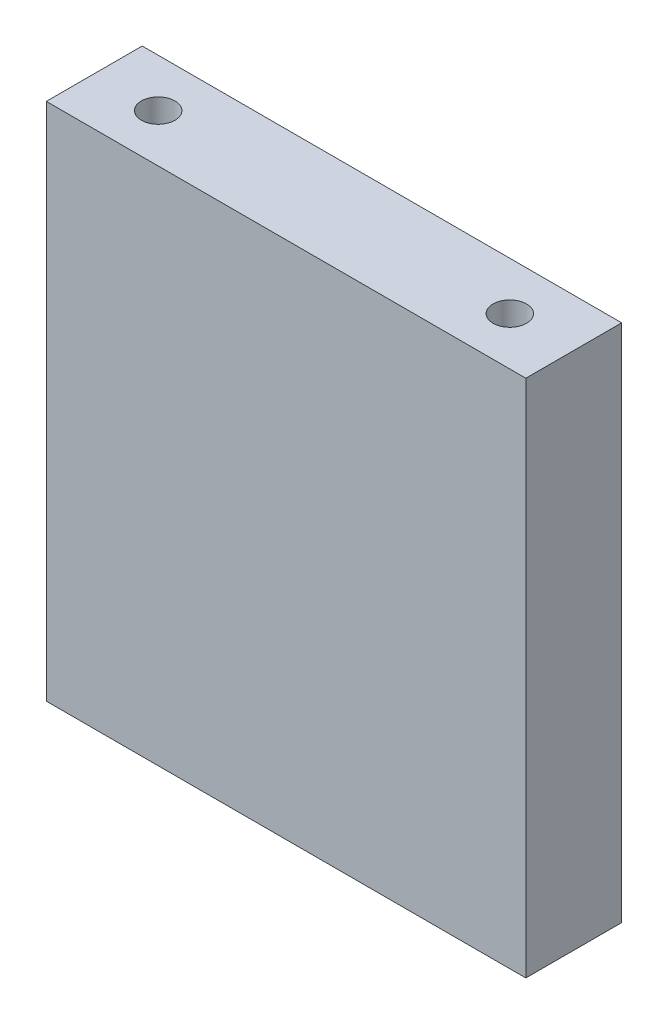
SolidWorks part; units mm, degrees
material "3.1325 (EN-AW 2017A)"
ref_plane "Plan de face" through (0, 0, 0) normal (0, 0, 1) x (1, 0, 0)
ref_plane "Plan de dessus" through (0, 0, 0) normal (0, 1, 0) x (1, 0, 0)
ref_plane "Plan de droite" through (0, 0, 0) normal (1, 0, 0) x (0, 0, -1)
sketch "Esquisse1" plane through (0, 0, 0) normal (0, 0, 1) x (1, 0, 0)
  line L1 (0, 0) -> (60, 0)
  line L2 (0, 0) -> (0, 65)
  line L3 (0, 65) -> (60, 65)
  line L4 (60, 0) -> (60, 65)
  dimension "D1" = 60
  dimension "D2" = 65
extrude "Boss.-Extru.1" add sketch "Esquisse1" along normal blind 12
hole_wizard "Trou taraudé M57" positions "Esquisse3" profile "Esquisse2" tap size "M5" standard "ISO"
sketch "Esquisse3" plane through (0, 65, 0) normal (0, 1, 0) x (-1, 0, 0)
  line L0 (-60, 0) -> (0, 0) construction
  line L1 (0, 12) -> (0, 0) construction
  point P0 (-8, 6)
  dimension "D1" = 6
  dimension "D2" = 8
sketch "Esquisse2" plane through (8, 65, 6) normal (1, 0, 0) x (0, 0, 1)
  line L0 (0, 0) -> (0, 15.2618)
  line L1 (0, 15.2618) -> (2.1, 14)
  line L2 (2.1, 14) -> (2.1, 0)
  line L5 (2.1, 0) -> (0, 0)
  line L10 (0, 15.2618) -> (-2.1, 14) construction
  line L11 (0, -6.35) -> (0, 107.95) construction
  dimension "Diamètre du trou pour taraudage" = 4.2
  dimension "Profondeur du trou pour taraudage" = 14
  dimension "Angle de pointe" = 118
cosmetic thread "Filetage de perçage1" parameters "D1"=10, "D2"=5
hole_wizard "Trou taraudé M58" positions "Esquisse5" profile "Esquisse4" tap size "M5" standard "ISO"
sketch "Esquisse5" plane through (0, 65, 0) normal (0, 1, 0) x (-1, 0, 0)
  line L0 (-60, 0) -> (0, 0) construction
  line L1 (-60, 12) -> (-60, 0) construction
  point P0 (-52, 6)
  dimension "D1" = 6
  dimension "D2" = 8
sketch "Esquisse4" plane through (52, 65, 6) normal (1, 0, 0) x (0, 0, 1)
  line L0 (0, 0) -> (0, 15.2618)
  line L1 (0, 15.2618) -> (2.1, 14)
  line L2 (2.1, 14) -> (2.1, 0)
  line L5 (2.1, 0) -> (0, 0)
  line L10 (0, 15.2618) -> (-2.1, 14) construction
  line L11 (0, -6.35) -> (0, 107.95) construction
  dimension "Diamètre du trou pour taraudage" = 4.2
  dimension "Profondeur du trou pour taraudage" = 14
  dimension "Angle de pointe" = 118
cosmetic thread "Filetage de perçage2" parameters "D1"=10, "D2"=5
hole_wizard "Trou taraudé M56" positions "Esquisse10" profile "Esquisse9" tap size "M5" standard "ISO"
sketch "Esquisse10" plane through (0, 0, 0) normal (0, -1, 0) x (1, 0, 0)
  line L0 (0, 12) -> (0, 0) construction
  line L1 (0, 12) -> (60, 12) construction
  point P0 (8, 6)
  dimension "D1" = 8
  dimension "D2" = 6
sketch "Esquisse9" plane through (8, 0, 6) normal (1, 0, 0) x (0, 0, -1)
  line L0 (0, 0) -> (0, 15.2618)
  line L1 (0, 15.2618) -> (2.1, 14)
  line L2 (2.1, 14) -> (2.1, 0)
  line L5 (2.1, 0) -> (0, 0)
  line L10 (0, 15.2618) -> (-2.1, 14) construction
  line L11 (0, -6.35) -> (0, 107.95) construction
  dimension "Diamètre du trou pour taraudage" = 4.2
  dimension "Profondeur du trou pour taraudage" = 14
  dimension "Angle de pointe" = 118
cosmetic thread "Filetage de perçage3" parameters "D1"=10, "D2"=5
hole_wizard "Trou taraudé M55" positions "Esquisse12" profile "Esquisse11" tap size "M5" standard "ISO"
sketch "Esquisse12" plane through (0, 0, 0) normal (0, -1, 0) x (1, 0, 0)
  line L0 (0, 12) -> (60, 12) construction
  line L1 (60, 12) -> (60, 0) construction
  point P0 (52, 6)
  dimension "D1" = 6
  dimension "D2" = 8
sketch "Esquisse11" plane through (52, 0, 6) normal (1, 0, 0) x (0, 0, -1)
  line L0 (0, 0) -> (0, 15.2618)
  line L1 (0, 15.2618) -> (2.1, 14)
  line L2 (2.1, 14) -> (2.1, 0)
  line L5 (2.1, 0) -> (0, 0)
  line L10 (0, 15.2618) -> (-2.1, 14) construction
  line L11 (0, -6.35) -> (0, 107.95) construction
  dimension "Diamètre du trou pour taraudage" = 4.2
  dimension "Profondeur du trou pour taraudage" = 14
  dimension "Angle de pointe" = 118
cosmetic thread "Filetage de perçage4" parameters "D1"=10, "D2"=5
